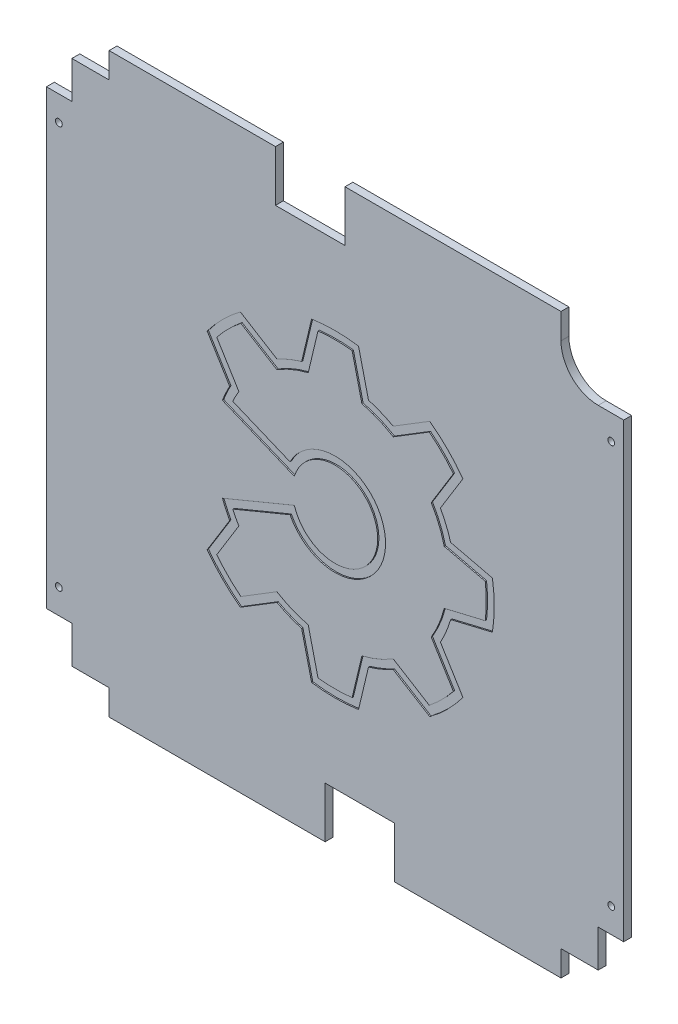
SolidWorks part; units mm, degrees
material "Acrylic (Medium-high impact)"
ref_plane "Front Plane" through (0, 0, 0) normal (0, 0, 1) x (1, 0, 0)
ref_plane "Top Plane" through (0, 0, 0) normal (0, 1, 0) x (1, 0, 0)
ref_plane "Right Plane" through (0, 0, 0) normal (1, 0, 0) x (0, 0, -1)
sketch "Sketch1" plane through (0, 0, 0) normal (0, 0, 1) x (1, 0, 0)
  line L0 (182, -212) -> (212, -212)
  line L1 (-182, -232.5) -> (-8, -232.5)
  line L2 (-232.5, -182) -> (-232.5, 0)
  line L3 (212, -212) -> (212, -182)
  line L4 (232.5, -182) -> (232.5, 0)
  line L5 (48, -232.5) -> (182, -232.5)
  line L6 (-232.5, 0) -> (232.5, 0) construction
  line L7 (-182, -212) -> (-212, -212)
  line L8 (-212, -212) -> (-212, -182)
  line L9 (232.5, 182) -> (232.5, 0)
  line L10 (232.5, 182) -> (212, 182)
  line L11 (212, 212) -> (212, 182)
  line L12 (182, 212) -> (212, 212)
  line L13 (182, 232.5) -> (182, 212)
  line L14 (182, 232.5) -> (8, 232.5)
  line L15 (8, 232.5) -> (8, 191.5)
  line L16 (-48, 191.5) -> (8, 191.5)
  line L17 (-48, 232.5) -> (-48, 191.5)
  line L18 (-48, 232.5) -> (-182, 232.5)
  line L19 (-182, 232.5) -> (-182, 212)
  line L20 (-182, 212) -> (-212, 212)
  line L21 (232.5, -182) -> (212, -182)
  line L22 (182, -232.5) -> (182, -212)
  line L23 (-212, 212) -> (-212, 182)
  line L24 (48, -232.5) -> (48, -191.5)
  line L25 (48, -191.5) -> (-8, -191.5)
  line L26 (-8, -232.5) -> (-8, -191.5)
  line L27 (-232.5, 182) -> (-212, 182)
  line L28 (-232.5, 182) -> (-232.5, 0)
  line L29 (-232.5, -182) -> (-212, -182)
  line L30 (-182, -232.5) -> (-182, -212)
  line L31 (0, 0) -> (0, -232.5) construction
  circle A0 centre (-222.5, -162) radius 2.75
  circle A1 centre (222.5, -162) radius 2.75
  circle A2 centre (222.5, 162) radius 2.75
  circle A3 centre (-222.5, 162) radius 2.75
  point P0 (0, 0)
  point P3 (0, 0)
  point P38 (0, 0)
  point P40 (20, -191.5)
  point P68 (0, 0)
  dimension "D21" = 20.5
  dimension "D22" = 20.5
  dimension "D23" = 232.5
  dimension "D7" = 5.5
  dimension "D8" = 10
  dimension "D9" = 20
  dimension "D3" = 50.5
  dimension "D4" = 20.5
  dimension "D5" = 20.5
  dimension "D6" = 2
  dimension "D10" = 20
  dimension "D11" = 50.5
  dimension "D12" = 50.5
  dimension "D15" = 56
  dimension "D16" = 41
  dimension "D18" = 50.5
  dimension "D20" = 465
extrude "Boss-Extrude1" add sketch "Sketch1" along normal blind 6.35
sketch "Sketch2" plane through (0, 0, 6.35) normal (0, 0, 1) x (1, 0, 0)
  line L0 (232.5, 182) -> (212, 182) construction
  line L1 (212, 212) -> (182, 212) construction
  line L2 (212, 182) -> (212, 212) construction
  line L3 (212, 212) -> (182, 212)
  line L4 (212, 182) -> (212, 212)
  arc A0 (182, 212) -> (212, 182) centre (212, 212) ccw
extrude "Cut-Extrude1" cut sketch "Sketch2" against normal up to surface (6.35 mm away) contours A0 L4 L3 up to face at (225.25, 162, 0)
sketch "Sketch3" plane through (0, 0, 6.35) normal (0, 0, 1) x (1, 0, 0)
  line L0 (0, 0) -> (125, 0) construction
  line L1 (0, 0) -> (123.9306, -16.3158) construction
  line L2 (0, 0) -> (115.4849, -47.8354) construction
  line L3 (0, 0) -> (120.7407, -32.3524) construction
  line L4 (123.9306, -16.3158) -> (90.5555, -24.2643) construction
  line L5 (123.9306, 16.3158) -> (90.5555, 24.2643) construction
  line L6 (76.0952, -99.1692) -> (46.875, -81.1899) construction
  line L7 (99.1692, -76.0952) -> (81.1899, -46.875) construction
  line L8 (-16.3158, -123.9306) -> (-24.2643, -90.5555) construction
  line L9 (16.3158, -123.9306) -> (24.2643, -90.5555) construction
  line L10 (-99.1692, -76.0952) -> (-81.1899, -46.875) construction
  line L11 (-76.0952, -99.1692) -> (-46.875, -81.1899) construction
  line L12 (-82.4139, 37.5736) -> (-36.2491, 18.4515)
  line L13 (-95.3084, 75.8792) -> (-77.4822, 46.9078)
  line L14 (-76.0952, 99.1692) -> (-46.875, 81.1899) construction
  line L15 (-99.1692, 76.0952) -> (-81.1899, 46.875) construction
  line L16 (16.3158, 123.9306) -> (24.2643, 90.5555) construction
  line L17 (-16.3158, 123.9306) -> (-24.2643, 90.5555) construction
  line L18 (99.1692, 76.0952) -> (81.1899, 46.875) construction
  line L19 (76.0952, 99.1692) -> (46.875, 81.1899) construction
  line L20 (0, 0) -> (88.3883, -88.3883) construction
  line L21 (0, 0) -> (0, -125) construction
  line L22 (0, 0) -> (-88.3883, -88.3883) construction
  line L23 (0, 0) -> (-125, 0) construction
  line L24 (0, 0) -> (-88.3883, 88.3883) construction
  line L25 (0, 0) -> (0, 125) construction
  line L26 (0, 0) -> (88.3883, 88.3883) construction
  line L27 (-86.6137, 35.8766) -> (-34.6455, 14.3506) construction
  line L28 (-86.6137, -35.8766) -> (-34.6455, -14.3506) construction
  line L29 (-75.8792, 95.3084) -> (-46.9078, 77.4822)
  line L30 (-123.9306, 16.3158) -> (-90.5555, 24.2643) [skipped]
  line L31 (-123.9306, -16.3158) -> (-90.5555, -24.2643) [skipped]
  line L32 (-13.7385, 121.0479) -> (-21.6193, 87.957)
  line L33 (13.7385, 121.0479) -> (21.6193, 87.957)
  line L34 (75.8792, 95.3084) -> (46.9078, 77.4822)
  line L35 (95.3084, 75.8792) -> (77.4822, 46.9078)
  line L36 (121.0479, 13.7385) -> (87.957, 21.6193)
  line L37 (121.0479, -13.7385) -> (87.957, -21.6193)
  line L38 (95.3084, -75.8792) -> (77.4822, -46.9078)
  line L39 (75.8792, -95.3084) -> (46.9078, -77.4822)
  line L40 (13.7385, -121.0479) -> (21.6193, -87.957)
  line L41 (-13.7385, -121.0479) -> (-21.6193, -87.957)
  line L42 (-75.8792, -95.3084) -> (-46.9078, -77.4822)
  line L43 (-95.3084, -75.8792) -> (-77.4822, -46.9078)
  line L44 (-82.4139, -37.5736) -> (-36.2491, -18.4515)
  line L45 (-90.714, 34.1384) -> (-32.7912, 10.146)
  line L46 (-103.0085, 76.2763) -> (-84.8748, 46.8052)
  line L47 (-76.2763, 103.0085) -> (-46.8052, 84.8748)
  line L48 (-18.9025, 126.7735) -> (-26.9193, 93.1118)
  line L49 (18.9025, 126.7735) -> (26.9193, 93.1118)
  line L50 (76.2763, 103.0085) -> (46.8052, 84.8748)
  line L51 (103.0085, 76.2763) -> (84.8748, 46.8052)
  line L52 (126.7735, 18.9025) -> (93.1118, 26.9193)
  line L53 (126.7735, -18.9025) -> (93.1118, -26.9193)
  line L54 (103.0085, -76.2763) -> (84.8748, -46.8052)
  line L55 (76.2763, -103.0085) -> (46.8052, -84.8748)
  line L56 (18.9025, -126.7735) -> (26.9193, -93.1118)
  line L57 (-18.9025, -126.7735) -> (-26.9193, -93.1118)
  line L58 (-76.2763, -103.0085) -> (-46.8052, -84.8748)
  line L59 (-103.0085, -76.2763) -> (-84.8748, -46.8052)
  line L60 (-90.714, -34.1384) -> (-32.7912, -10.146)
  line L61 (3.4925, 0) -> (-3.4925, 0) construction
  arc A0 (-34.6455, -14.3506) -> (-34.6455, 14.3506) centre (0, 0) ccw construction
  arc A1 (99.1692, 76.0952) -> (76.0952, 99.1692) centre (0, 0) ccw construction
  arc A2 (-36.2491, -18.4515) -> (-36.2491, 18.4515) centre (0, 0) ccw
  arc A3 (90.5555, 24.2643) -> (81.1899, 46.875) centre (0, 0) ccw construction
  arc A4 (81.1899, -46.875) -> (90.5555, -24.2643) centre (0, 0) ccw construction
  arc A5 (24.2643, -90.5555) -> (46.875, -81.1899) centre (0, 0) ccw construction
  arc A6 (-46.875, -81.1899) -> (-24.2643, -90.5555) centre (0, 0) ccw construction
  arc A7 (-86.6137, -35.8766) -> (-81.1899, -46.875) centre (0, 0) ccw construction
  arc A8 (-81.1899, 46.875) -> (-86.6137, 35.8766) centre (0, 0) ccw construction
  arc A9 (-24.2643, 90.5555) -> (-46.875, 81.1899) centre (0, 0) ccw construction
  arc A10 (46.875, 81.1899) -> (24.2643, 90.5555) centre (0, 0) ccw construction
  arc A11 (115.4849, -47.8354) -> (120.7407, -32.3524) centre (0, 0) ccw construction
  arc A12 (123.9306, -16.3158) -> (123.9306, 16.3158) centre (0, 0) ccw construction
  arc A13 (76.0952, -99.1692) -> (99.1692, -76.0952) centre (0, 0) ccw construction
  arc A14 (-16.3158, -123.9306) -> (16.3158, -123.9306) centre (0, 0) ccw construction
  arc A15 (-99.1692, -76.0952) -> (-76.0952, -99.1692) centre (0, 0) ccw construction
  arc A16 (-77.4822, 46.9078) -> (-82.4139, 37.5736) centre (0, 0) ccw
  arc A17 (-76.0952, 99.1692) -> (-99.1692, 76.0952) centre (0, 0) ccw construction
  arc A18 (16.3158, 123.9306) -> (-16.3158, 123.9306) centre (0, 0) ccw construction
  arc A19 (-75.8792, 95.3084) -> (-95.3084, 75.8792) centre (0, 0) ccw
  arc A20 (-21.6193, 87.957) -> (-46.9078, 77.4822) centre (0, 0) ccw
  arc A21 (13.7385, 121.0479) -> (-13.7385, 121.0479) centre (0, 0) ccw
  arc A22 (46.9078, 77.4822) -> (21.6193, 87.957) centre (0, 0) ccw
  arc A23 (95.3084, 75.8792) -> (75.8792, 95.3084) centre (0, 0) ccw
  arc A24 (87.957, 21.6193) -> (77.4822, 46.9078) centre (0, 0) ccw
  arc A25 (121.0479, -13.7385) -> (121.0479, 13.7385) centre (0, 0) ccw
  arc A26 (77.4822, -46.9078) -> (87.957, -21.6193) centre (0, 0) ccw
  arc A27 (75.8792, -95.3084) -> (95.3084, -75.8792) centre (0, 0) ccw
  arc A28 (21.6193, -87.957) -> (46.9078, -77.4822) centre (0, 0) ccw
  arc A29 (-13.7385, -121.0479) -> (13.7385, -121.0479) centre (0, 0) ccw
  arc A30 (-46.9078, -77.4822) -> (-21.6193, -87.957) centre (0, 0) ccw
  arc A31 (-95.3084, -75.8792) -> (-75.8792, -95.3084) centre (0, 0) ccw
  arc A32 (-82.4139, -37.5736) -> (-77.4822, -46.9078) centre (0, 0) ccw
  arc A33 (-32.7912, -10.146) -> (-32.7912, 10.146) centre (0, 0) ccw
  arc A34 (-84.8748, 46.8052) -> (-90.714, 34.1384) centre (0, 0) ccw
  arc A35 (-76.2763, 103.0085) -> (-103.0085, 76.2763) centre (0, 0) ccw
  arc A36 (-26.9193, 93.1118) -> (-46.8052, 84.8748) centre (0, 0) ccw
  arc A37 (18.9025, 126.7735) -> (-18.9025, 126.7735) centre (0, 0) ccw
  arc A38 (46.8052, 84.8748) -> (26.9193, 93.1118) centre (0, 0) ccw
  arc A39 (103.0085, 76.2763) -> (76.2763, 103.0085) centre (0, 0) ccw
  arc A40 (93.1118, 26.9193) -> (84.8748, 46.8052) centre (0, 0) ccw
  arc A41 (126.7735, -18.9025) -> (126.7735, 18.9025) centre (0, 0) ccw
  arc A42 (84.8748, -46.8052) -> (93.1118, -26.9193) centre (0, 0) ccw
  arc A43 (76.2763, -103.0085) -> (103.0085, -76.2763) centre (0, 0) ccw
  arc A44 (26.9193, -93.1118) -> (46.8052, -84.8748) centre (0, 0) ccw
  arc A45 (-18.9025, -126.7735) -> (18.9025, -126.7735) centre (0, 0) ccw
  arc A46 (-46.8052, -84.8748) -> (-26.9193, -93.1118) centre (0, 0) ccw
  arc A47 (-103.0085, -76.2763) -> (-76.2763, -103.0085) centre (0, 0) ccw
  arc A48 (-90.714, -34.1384) -> (-84.8748, -46.8052) centre (0, 0) ccw
  point P44 (0, 0)
  dimension "D3" = 250
  dimension "D4" = 187.5
  dimension "D5" = 75
  dimension "D1" = 22.5
  dimension "D2" = 7.5
  dimension "D6" = 15
  dimension "D8" = 22.5
  dimension "D9" = 22.5
  dimension "D10" = 3.175
  dimension "D11" = 3.175
  dimension "D7" = 8
extrude "Cut-Extrude2" cut sketch "Sketch3" against normal blind 1
equation "\"D4@Sketch3\"=.75*\"D3@Sketch3\""
equation "\"D5@Sketch3\"=.3*\"D3@Sketch3\""
equation "\"D2@Sketch3\"=\"D1@Sketch3\"/3"
equation "\"D6@Sketch3\"=\"D1@Sketch3\"*(2/3)"
